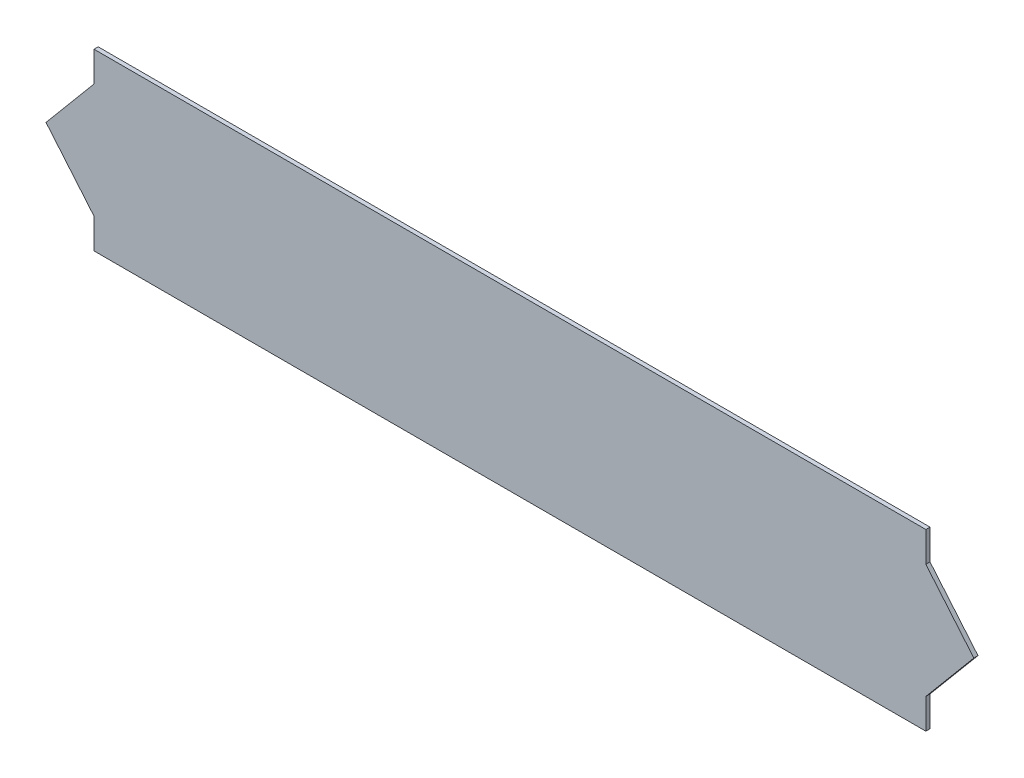
SolidWorks part; units mm, degrees
material "6061-T6 (SS)"
ref_plane "Front Plane" through (0, 0, 0) normal (0, 0, 1) x (1, 0, 0)
ref_plane "Top Plane" through (0, 0, 0) normal (0, 1, 0) x (1, 0, 0)
ref_plane "Right Plane" through (0, 0, 0) normal (1, 0, 0) x (0, 0, -1)
sketch "Sketch1" plane through (0, 0, 0) normal (0, 0, 1) x (1, 0, 0)
  line L0 (0, 0) -> (0, -115.4705) construction
  line L1 (200, 0) -> (-200, 0)
  line L2 (-200, 0) -> (-200, -14.5)
  line L3 (-200, -14.5) -> (-223.0752, -42)
  line L4 (-223.0752, -42) -> (-200, -69.5)
  line L5 (-200, -69.5) -> (-200, -84)
  line L6 (-200, -84) -> (200, -84)
  line L7 (200, -69.5) -> (200, -84)
  line L8 (223.0752, -42) -> (200, -69.5)
  line L9 (200, -14.5) -> (223.0752, -42)
  line L10 (200, 0) -> (200, -14.5)
  point P11 (0, -84)
  dimension "D1" = 200
  dimension "D2" = 14.5
  dimension "D3" = 14.5
  dimension "D4" = 200
  dimension "D5" = 55
  dimension "D6" = 100
extrude "Boss-Extrude1" add sketch "Sketch1" along normal blind 2
